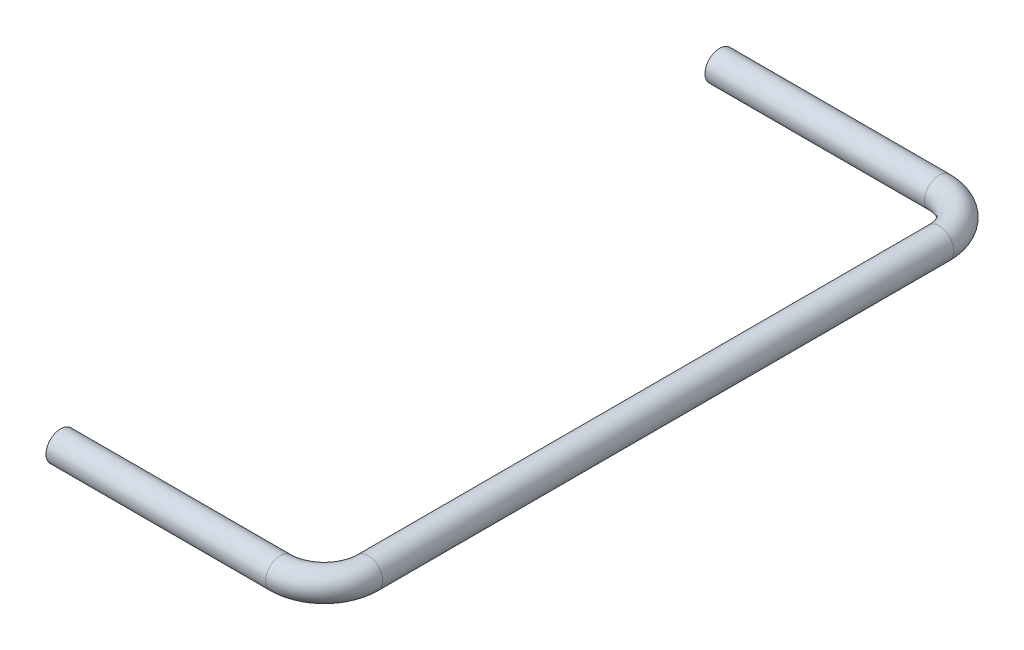
SolidWorks part; units mm, degrees
ref_plane "Спереди" through (0, 0, 0) normal (0, 0, 1) x (1, 0, 0)
ref_plane "Сверху" through (0, 0, 0) normal (0, 1, 0) x (1, 0, 0)
ref_plane "Справа" through (0, 0, 0) normal (1, 0, 0) x (0, 0, -1)
sketch "Эскиз1" plane through (0, 0, 0) normal (1, 0, 0) x (0, 0, -1)
  circle A0 centre (0, 0) radius 1
sketch3d "Трехмерный эскиз1"
  line L0 (0, 0, 0) -> (15, 0, 0)
  line L1 (18, 0, -3) -> (18, 0, -42)
  line L2 (15, 0, -45) -> (0, 0, -45)
  arc A0 (15, 0, 0) -> (18, 0, -3) centre (15, 0, -3) ccw
  arc A1 (18, 0, -42) -> (15, 0, -45) centre (15, 0, -42) ccw
  point P7 (18, 0, 0)
  point P8 (15, 3, -3)
  point P11 (18, 0, -45)
  point P12 (15, 3, -42)
  dimension "D1" = 3
sweep "По траектории1" add profiles "Эскиз1" path "Трехмерный эскиз1"
